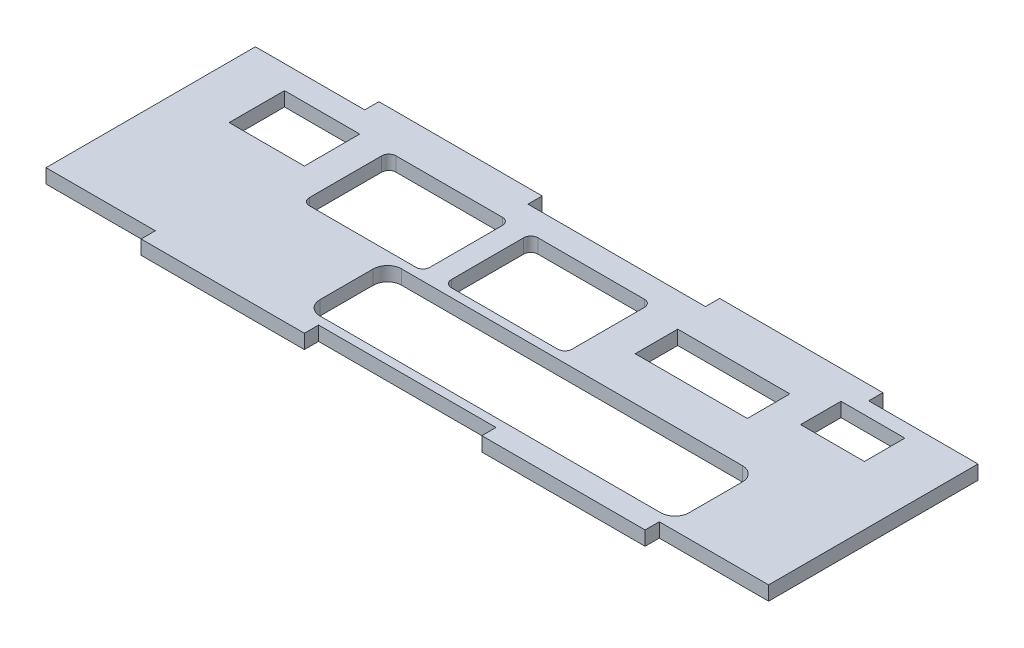
SolidWorks part; units mm, degrees
ref_plane "前视基准面" through (0, 0, 0) normal (0, 0, 1) x (1, 0, 0)
ref_plane "上视基准面" through (0, 0, 0) normal (0, 1, 0) x (1, 0, 0)
ref_plane "右视基准面" through (0, 0, 0) normal (1, 0, 0) x (0, 0, -1)
sketch "草图1" plane through (0, 0, 0) normal (0, 1, 0) x (1, 0, 0)
  line L1 (-50.9, 14.75) -> (50.9, 14.75)
  line L2 (-50.9, 14.75) -> (-50.9, -14.75)
  line L3 (-50.9, -14.75) -> (50.9, -14.75)
  line L4 (50.9, 14.75) -> (50.9, -14.75)
  line L5 (-50.9, 14.75) -> (50.9, -14.75) construction
  line L6 (-50.9, -14.75) -> (50.9, 14.75) construction
  point P0 (0, 0)
  dimension "D1" = 101.8
  dimension "D2" = 29.5
extrude "凸台-拉伸1" add sketch "草图1" along normal blind 2
sketch "草图2" plane through (0, 2, 0) normal (0, 1, 0) x (1, 0, 0)
  line L0 (50.9, 14.75) -> (-50.9, 14.75) construction
  line L1 (-35.5, 14.75) -> (-12.5, 14.75)
  line L2 (-35.5, 14.75) -> (-35.5, 16.75)
  line L3 (-35.5, 16.75) -> (-12.5, 16.75)
  line L4 (-12.5, 14.75) -> (-12.5, 16.75)
  line L5 (0, 0) -> (11.3635, 0) construction
  line L6 (12.5, 14.75) -> (35.5, 14.75)
  line L7 (12.5, 14.75) -> (12.5, 16.75)
  line L8 (12.5, 16.75) -> (35.5, 16.75)
  line L9 (35.5, 14.75) -> (35.5, 16.75)
  line L10 (35.5, -14.75) -> (35.5, -16.75)
  line L11 (12.5, -16.75) -> (35.5, -16.75)
  line L12 (12.5, -14.75) -> (12.5, -16.75)
  line L13 (12.5, -14.75) -> (35.5, -14.75)
  line L14 (-12.5, -14.75) -> (-12.5, -16.75)
  line L15 (-35.5, -16.75) -> (-12.5, -16.75)
  line L16 (-35.5, -14.75) -> (-35.5, -16.75)
  line L17 (-35.5, -14.75) -> (-12.5, -14.75)
  dimension "D1" = 23
  dimension "D2" = 23
  dimension "D3" = 12.5
  dimension "D4" = 12.5
  dimension "D5" = 2
  dimension "D6" = 2
extrude "凸台-拉伸2" add sketch "草图2" against normal blind 2
sketch "草图3" plane through (0, 2, 0) normal (0, 1, 0) x (1, 0, 0)
  line L2 (50.9, -14.75) -> (50.9, 14.75) construction
  line L3 (33.6, 12.75) -> (42.6, 12.75)
  line L4 (33.6, 12.75) -> (33.6, 7.05)
  line L5 (33.6, 7.05) -> (42.6, 7.05)
  line L6 (42.6, 12.75) -> (42.6, 7.05)
  line L7 (50.9, 14.75) -> (35.5, 14.75) construction
  dimension "D2" = 2
  dimension "D1" = 17.3
  dimension "D3" = 9
  dimension "D4" = 5.7
extrude "切除-拉伸1" cut sketch "草图3" against normal through all
sketch "草图4" plane through (0, 2, 0) normal (0, 1, 0) x (1, 0, 0)
  line L2 (-35.5, 14.75) -> (-50.9, 14.75) construction
  line L3 (-43.5, 11.45) -> (-32.9, 11.45)
  line L4 (-43.5, 11.45) -> (-43.5, 3.65)
  line L5 (-43.5, 3.65) -> (-32.9, 3.65)
  line L6 (-32.9, 11.45) -> (-32.9, 3.65)
  line L7 (-50.9, 14.75) -> (-50.9, -14.75) construction
  dimension "D3" = 7.8
  dimension "D1" = 11.1
  dimension "D2" = 7.4
  dimension "D4" = 10.6
extrude "切除-拉伸2" cut sketch "草图4" against normal through all
sketch "草图6" plane through (0, 2, 0) normal (0, 1, 0) x (1, 0, 0)
  line L0 (12.5, 14.75) -> (-12.5, 14.75) construction
  line L1 (-28.7, 11.35) -> (-11.7, 11.35)
  line L2 (-28.7, 11.35) -> (-28.7, -0.85)
  line L3 (-28.7, -0.85) -> (-11.7, -0.85)
  line L4 (-11.7, 11.35) -> (-11.7, -0.85)
  line L5 (-50.9, 14.75) -> (-50.9, -14.75) construction
  dimension "D1" = 3.4
  dimension "D2" = 12.2
  dimension "D3" = 22.2
  dimension "D4" = 17
extrude "切除-拉伸4" cut sketch "草图6" against normal through all
fillet "圆角1" radius 1 4 edges at (-11.7, 1, -11.35) (-11.7, 1, 0.85) (-28.7, 1, 0.85) (-28.7, 1, -11.35)
pattern_linear "阵列(线性)1" count 2 spacing 20 along (1, 0, 0) of "圆角1", "切除-拉伸4"
sketch "草图7" plane through (0, 2, 0) normal (0, 1, 0) x (1, 0, 0)
  line L0 (-8.7, 10.35) -> (-8.7, 0.15) construction
  line L1 (13.3, 10.05) -> (29.1, 10.05)
  line L2 (13.3, 10.05) -> (13.3, 4.05)
  line L3 (13.3, 4.05) -> (29.1, 4.05)
  line L4 (29.1, 10.05) -> (29.1, 4.05)
  line L5 (-7.7, -0.85) -> (7.3, -0.85) construction
  dimension "D1" = 22
  dimension "D2" = 15.8
  dimension "D3" = 6
  dimension "D4" = 4.9
extrude "切除-拉伸5" cut sketch "草图7" against normal through all
sketch "草图8" plane through (0, 2, 0) normal (0, 1, 0) x (1, 0, 0)
  line L552 (-12.5, -14.75) -> (12.5, -14.75) construction
  line L553 (-13.5, -2.05) -> (34.5, -2.05)
  line L554 (-15.5, -4.05) -> (-15.5, -11.55)
  line L555 (-13.5, -13.55) -> (34.5, -13.55)
  line L556 (36.5, -4.05) -> (36.5, -11.55)
  line L557 (-7.7, -0.85) -> (7.3, -0.85) construction
  line L558 (-12.5, -16.75) -> (-12.5, -14.75) construction
  line L559 (35.5, -16.75) -> (35.5, -14.75) construction
  arc A0 (34.5, -2.05) -> (36.5, -4.05) centre (34.5, -4.05) cw
  arc A1 (-15.5, -11.55) -> (-13.5, -13.55) centre (-13.5, -11.55) ccw
  arc A26 (34.5, -13.55) -> (36.5, -11.55) centre (34.5, -11.55) ccw
  arc A27 (-13.5, -2.05) -> (-15.5, -4.05) centre (-13.5, -4.05) ccw
  dimension "D5" = 2
  dimension "D1" = 1.2
  dimension "D2" = 1.2
  dimension "D3" = 3
  dimension "D4" = 1
extrude "切除-拉伸6" cut sketch "草图8" against normal through all
